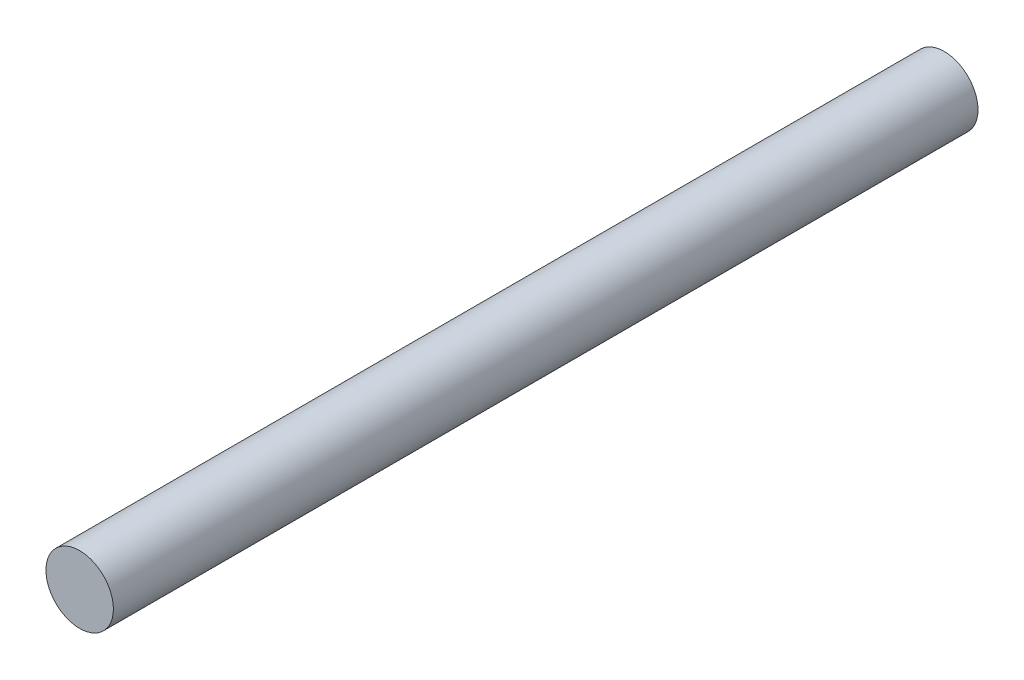
SolidWorks part; units mm, degrees
ref_plane "Front Plane" through (0, 0, 0) normal (0, 0, 1) x (1, 0, 0)
ref_plane "Top Plane" through (0, 0, 0) normal (0, 1, 0) x (1, 0, 0)
ref_plane "Right Plane" through (0, 0, 0) normal (1, 0, 0) x (0, 0, -1)
sketch "Sketch1" plane through (0, 0, 0) normal (0, 0, 1) x (1, 0, 0)
  circle A1 centre (0, 0) radius 39
  dimension "D2" = 78
extrude "Boss-Extrude1" add sketch "Sketch1" along normal mid plane 1000
